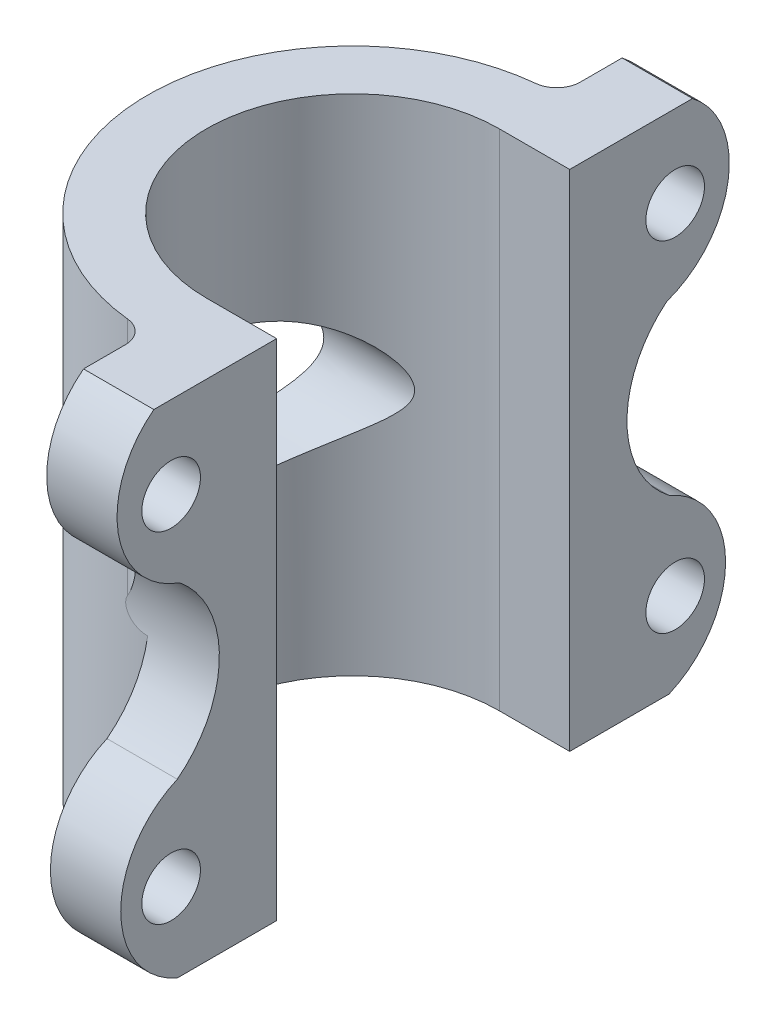
SolidWorks part; units mm, degrees
ref_plane "Front Plane" through (0, 0, 0) normal (0, 0, 1) x (1, 0, 0)
ref_plane "Top Plane" through (0, 0, 0) normal (0, 1, 0) x (1, 0, 0)
ref_plane "Right Plane" through (0, 0, 0) normal (1, 0, 0) x (0, 0, -1)
sketch "Sketch12" plane through (0, 0, 0) normal (0, 1, 0) x (1, 0, 0)
  line L1 (0, 35) -> (0, 52)
  line L2 (0, 52) -> (6, 52)
  line L3 (6, 52) -> (6, -17)
  line L4 (6, -17) -> (0, -17)
  line L5 (0, -17) -> (0, 0)
  arc A0 (0, 35) -> (0, 0) centre (0, 17.5) ccw
  dimension "D1" = 17.5
  dimension "D2" = 17
  dimension "D3" = 6
  dimension "D4" = 17
extrude "Boss-Extrude2" add sketch "Sketch12" along normal mid plane 43
sketch "Sketch13" plane through (0, -21.5, 0) normal (0, -1, 0) x (1, 0, 0)
  line L5 (0, -30) -> (6, -30)
  line L6 (6, 17) -> (6, -52) construction
  line L7 (6, -30) -> (6, -5)
  line L8 (6, -5) -> (0, -5)
  arc A3 (0, 0) -> (0, -35) centre (0, -17.5) ccw construction
  arc A4 (0, 0) -> (0, -35) centre (0, -17.5) ccw
  arc A5 (0, -5) -> (0, -30) centre (0, -17.5) ccw
  dimension "D2" = 5
extrude "Cut-Extrude8" cut sketch "Sketch13" against normal through all
ref_plane "Plane3" through (0, 0, -17.5) normal (0, 0, 1) x (1, 0, 0)
sketch "Sketch14" plane through (6, 0, 0) normal (1, 0, 0) x (0, 0, -1)
  line L1 (-17, -21.5) -> (5, -21.5) construction
  line L5 (-17, 21.5) -> (5, 21.5) construction
  line L7 (-3.475, -21.5) -> (-17, -21.5)
  line L8 (-17, -21.5) -> (-17, 21.5)
  line L9 (-17, 21.5) -> (-5.475, 21.5)
  arc A0 (-3.475, -21.5) -> (-3.475, -6.8145) centre (-0.2994, -14.1573) cw
  arc A2 (-3.475, -6.8145) -> (-3.2721, 7.5983) centre (-9.0789, 0.4722) ccw
  arc A3 (-3.2721, 7.5983) -> (-5.475, 21.5) centre (-0.6162, 15.1445) cw
  dimension "D1" = 9.1924
  dimension "D3" = 8
  dimension "D4" = 8
  dimension "D2" = 11.525
extrude "Cut-Extrude9" cut sketch "Sketch14" against normal through all
mirror "Mirror1" about plane through (0, 0, -17.5) normal (0, 0, 1) of "Cut-Extrude9"
sketch "Sketch18" plane through (0, 0, 0) normal (-1, 0, 0) x (0, 0, 1)
  line L0 (-17.5, -3.3) -> (-17.5, 3.3) construction
  circle A0 centre (-39, 14.5) radius 2.5
  circle A1 centre (4, 14.5) radius 2.5
  circle A2 centre (-39, -14.5) radius 2.5
  circle A3 centre (4, -14.5) radius 2.5
  dimension "D3" = 5
  dimension "D4" = 5
  dimension "D1" = 7
  dimension "D2" = 4
  dimension "D5" = 7
  dimension "D6" = 4
extrude "Cut-Extrude13" cut sketch "Sketch18" against normal through all both
sketch "Sketch19" plane through (0, 0, 0) normal (1, 0, 0) x (0, 0, -1)
  line L0 (17.5, 3.3) -> (17.5, -3.3) construction
  ellipse E0 centre (17.5, 0) end of major axis (28.5718, 0) minor radius 5.9543
  point P1 (6.4282, 0)
extrude "Cut-Extrude14" cut sketch "Sketch19" against normal through all both and the other way through all
fillet "Fillet6" radius 2 1 edges at (0, 11.706, 0)
fillet "Fillet7" radius 2 1 edges at (0, 11.706, -35)
